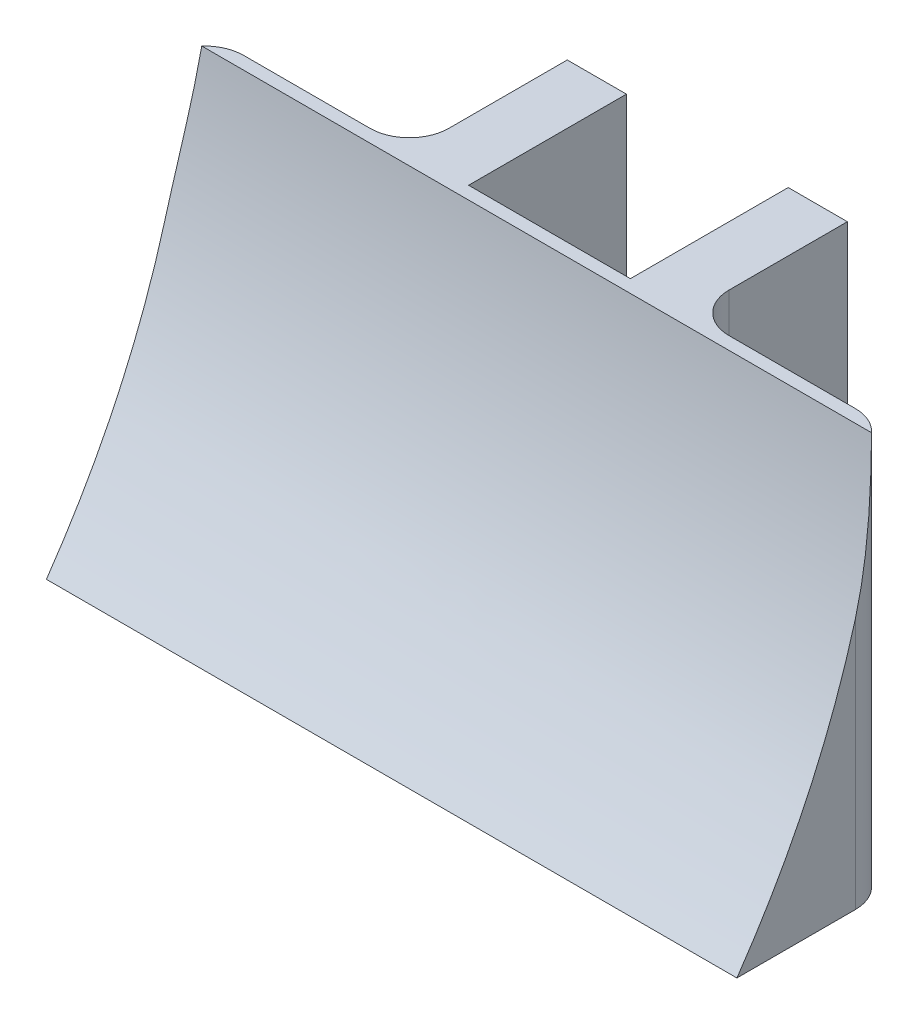
SolidWorks part; units mm, degrees
ref_plane "Front Plane" through (0, 0, 0) normal (0, 0, 1) x (1, 0, 0)
ref_plane "Top Plane" through (0, 0, 0) normal (0, 1, 0) x (1, 0, 0)
ref_plane "Right Plane" through (0, 0, 0) normal (1, 0, 0) x (0, 0, -1)
sketch "Sketch2" plane through (0, 0, 0) normal (0, 0, 1) x (1, 0, 0)
  line L0 (-5.6, 0) -> (5.6, 0)
  line L1 (-7.1, 10) -> (-4.1, 10)
  line L2 (-7.1, 10) -> (-7.1, -10)
  line L3 (-7.1, -10) -> (-4.1, -10)
  line L4 (-4.1, 10) -> (-4.1, -10)
  line L5 (-7.1, 10) -> (-4.1, -10) construction
  line L6 (-7.1, -10) -> (-4.1, 10) construction
  line L7 (7.1, 10) -> (4.1, 10)
  line L8 (7.1, 10) -> (7.1, -10)
  line L9 (7.1, -10) -> (4.1, -10)
  line L10 (4.1, 10) -> (4.1, -10)
  line L11 (7.1, 10) -> (4.1, -10) construction
  line L12 (7.1, -10) -> (4.1, 10) construction
  point P0 (-5.6, 0)
  point P5 (5.6, 0)
  point P10 (0, 0)
  dimension "D1" = 8.2
  dimension "D2" = 3
  dimension "D3" = 20
extrude "Boss-Extrude1" add sketch "Sketch2" along normal blind 8
sketch "Sketch3" plane through (0, 0, 8) normal (0, 0, 1) x (1, 0, 0)
  line L0 (7.1, -10) -> (4.1, -10) construction
  line L1 (-17.5, 10) -> (17.5, 10)
  line L2 (-17.5, 10) -> (-17.5, -10)
  line L3 (-17.5, -10) -> (17.5, -10)
  line L4 (17.5, 10) -> (17.5, -10)
  line L5 (-17.5, 10) -> (17.5, -10) construction
  line L6 (-17.5, -10) -> (17.5, 10) construction
  point P0 (0, 0)
  dimension "D1" = 35
extrude "Boss-Extrude2" add sketch "Sketch3" along normal blind 8
sketch "Sketch4" plane through (17.5, 0, 0) normal (1, 0, 0) x (0, 0, -1)
  line L0 (-16, 10) -> (-8, 10) construction
  line L1 (-8.6504, 10) -> (-18.7493, 11.1467)
  line L2 (-18.7493, 11.1467) -> (-17.5561, -8.149)
  line L3 (-17.5561, -8.149) -> (-16, -10)
  spline S0 degree 2 poles (-8.6504, 10) (-9.7606, -0.9933) (-16, -10) knots 0 0 0 1 1 1
extrude "Cut-Extrude1" cut sketch "Sketch4" against normal blind 100
fillet "Fillet1" radius 2 4 edges at (17.5, 0, 8) (-17.5, 0, 8) (-7.1, 0, 8) (7.1, 0, 8)
